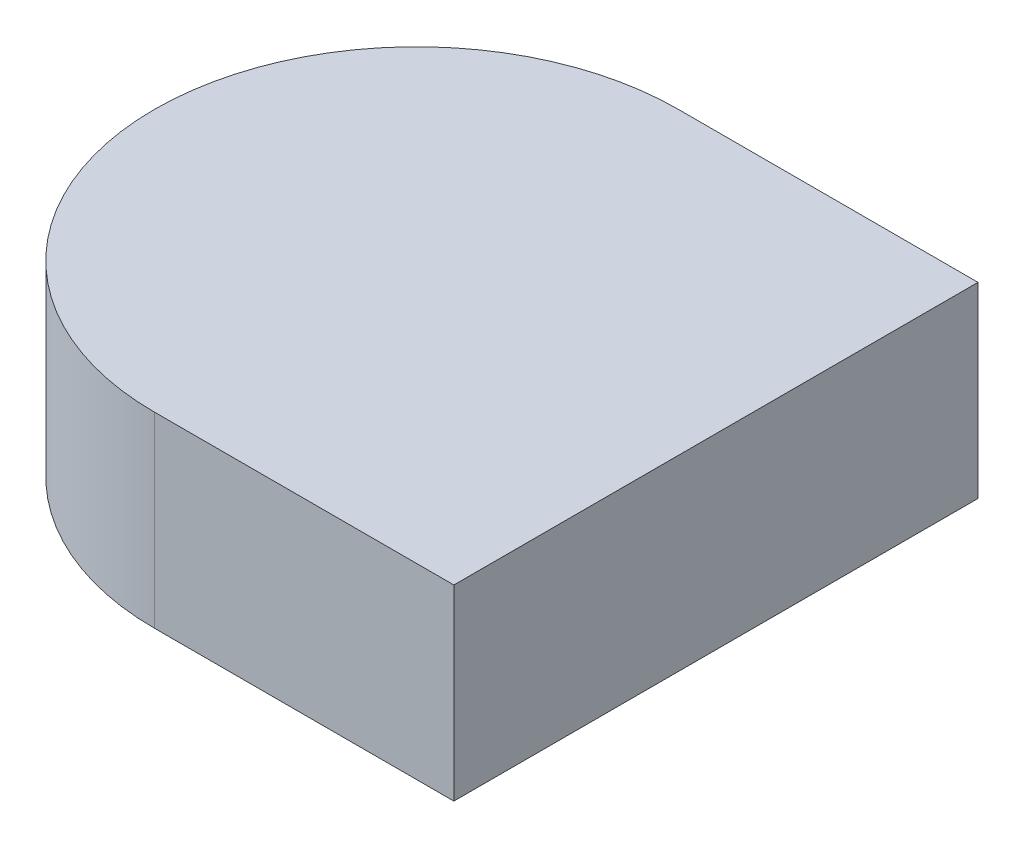
SolidWorks part; units mm, degrees
material "ABS"
ref_plane "Front Plane" through (0, 0, 0) normal (0, 0, 1) x (1, 0, 0)
ref_plane "Top Plane" through (0, 0, 0) normal (0, 1, 0) x (1, 0, 0)
ref_plane "Right Plane" through (0, 0, 0) normal (1, 0, 0) x (0, 0, -1)
sketch "Sketch1" plane through (0, 0, 0) normal (0, 0, 1) x (1, 0, 0)
  line L0 (-5.08, 0) -> (5.08, 0)
  line L1 (5.08, 0) -> (5.08, -3.175)
  line L2 (5.08, -3.175) -> (-5.08, -3.175)
  line L3 (-5.08, -3.175) -> (-5.08, 0)
  point P3 (0, -3.175)
  dimension "D1" = 10.16
  dimension "D2" = 3.175
extrude "Boss-Extrude1" add sketch "Sketch1" along normal mid plane 8.89
sketch "Sketch2" plane through (0, 0, 0) normal (0, 0, 1) x (1, 0, 0)
  line L0 (-1.27, 2.54) -> (-1.27, 3.3867)
  line L1 (1.27, 2.54) -> (1.27, 3.3867)
  line L2 (-2.3947, 3.3867) -> (-1.27, 3.3867)
  line L3 (1.27, 3.3867) -> (2.3947, 3.3867)
  line L4 (-1.27, 0.3403) -> (-1.27, 0)
  line L5 (5.08, 0) -> (-5.08, 0) construction
  line L6 (1.27, 0.3403) -> (1.27, 0)
  line L7 (-1.27, 0) -> (1.27, 0)
  arc A0 (-2.3947, 3.3867) -> (-1.27, 0.3403) centre (0, 2.54) ccw
  arc A1 (-1.27, 2.54) -> (1.27, 2.54) centre (0, 2.54) ccw
  arc A2 (1.27, 0.3403) -> (2.3947, 3.3867) centre (0, 2.54) ccw
  dimension "D1" = 5.08
  dimension "D2" = 2.54
extrude "Boss-Extrude2" [suppressed] add sketch "Sketch2" along normal mid plane 3.81
sketch "Sketch3" plane through (0, -3.175, 0) normal (0, -1, 0) x (1, 0, 0)
  line L0 (-2.54, 2.54) -> (-2.54, -2.54)
  line L1 (-2.54, -2.54) -> (2.54, -2.54)
  line L2 (2.54, -2.54) -> (2.54, 2.54)
  line L3 (2.54, 2.54) -> (-2.54, 2.54)
  line L4 (-5.08, -4.445) -> (5.08, -4.445)
  line L5 (5.08, -4.445) -> (5.08, 4.445)
  line L6 (5.08, 4.445) -> (-5.08, 4.445)
  line L7 (-5.08, 4.445) -> (-5.08, -4.445)
  line L8 (-5.08, -4.445) -> (5.08, -4.445)
  line L9 (5.08, -4.445) -> (5.08, 4.445)
  line L10 (5.08, 4.445) -> (-5.08, 4.445)
  line L11 (-5.08, 4.445) -> (-5.08, -4.445)
  dimension "D1" = 0
extrude "Cut-Extrude1" cut sketch "Sketch3" against normal blind 1.905 flip side to cut
sketch "Sketch4" plane through (0, 0, 0) normal (0, 1, 0) x (1, 0, 0)
  line L0 (-5.08, -4.445) -> (-5.08, 4.445) construction
  line L1 (-5.08, -4.445) -> (-5.08, 4.445)
  arc A0 (-5.08, 4.445) -> (-5.08, -4.445) centre (-5.08, 0) ccw
extrude "Boss-Extrude3" [suppressed] add sketch "Sketch4" against normal up to surface (6.35 mm away)
sketch "Sketch5" plane through (0, 0, 0) normal (0, 1, 0) x (1, 0, 0)
  line L0 (0, 4.445) -> (-5.08, 4.445)
  line L1 (-5.08, 4.445) -> (-5.08, -4.445)
  line L2 (93.98, -4.445) -> (-5.08, -4.445) construction
  line L3 (-5.08, -4.445) -> (-5.08, 4.445) construction
  line L4 (-5.08, -4.445) -> (0, -4.445)
  arc A0 (0, 4.445) -> (0, -4.445) centre (0, 0) ccw
extrude "Cut-Extrude2" cut sketch "Sketch5" against normal through all both and the other way through all
sketch "Sketch6" plane through (0, -1.27, 0) normal (0, -1, 0) x (1, 0, 0)
  circle A0 centre (0, 0) radius 1.5875
  dimension "D1" = 3.175
extrude "Cut-Extrude3" cut sketch "Sketch6" against normal blind 0.2032
